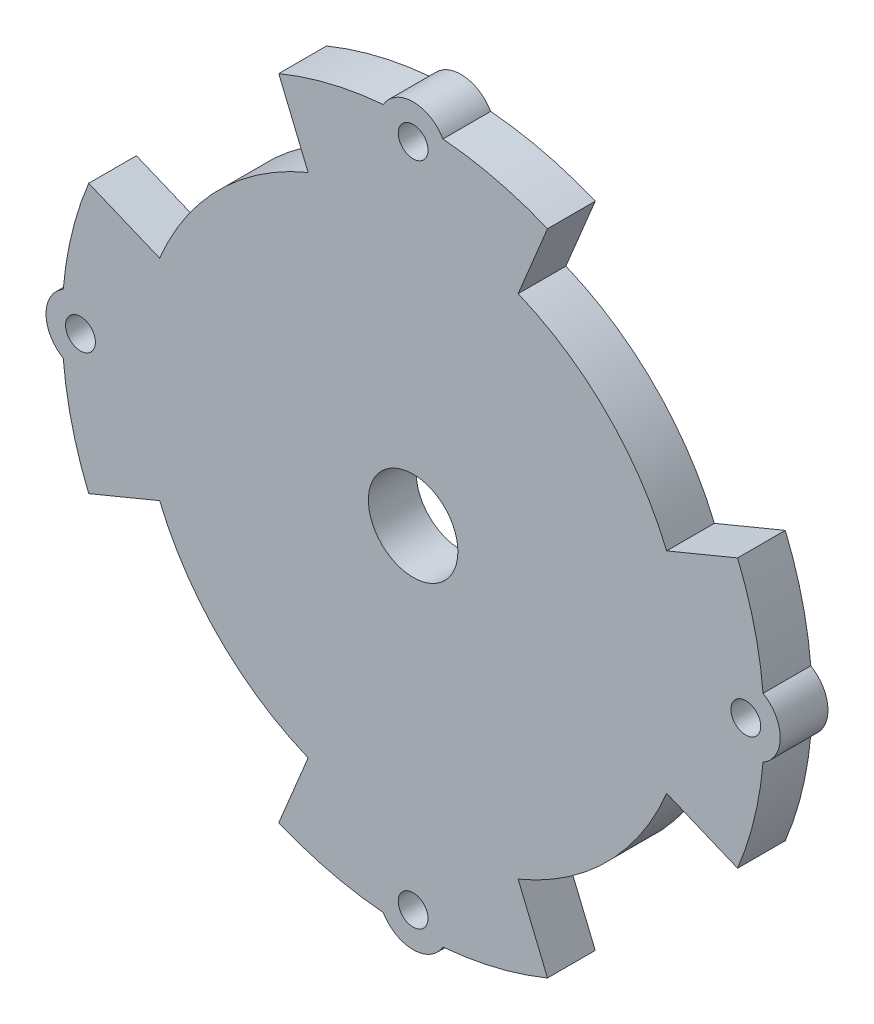
SolidWorks part; units mm, degrees
ref_plane "Front Plane" through (0, 0, 0) normal (0, 0, 1) x (1, 0, 0)
ref_plane "Top Plane" through (0, 0, 0) normal (0, 1, 0) x (1, 0, 0)
ref_plane "Right Plane" through (0, 0, 0) normal (1, 0, 0) x (0, 0, -1)
sketch "Sketch1" plane through (0, 0, 0) normal (0, 0, 1) x (1, 0, 0)
  line L0 (20, 0) -> (25, 0) construction
  line L1 (-20, 0) -> (-23, 0) construction
  line L2 (0, 25) -> (2.5, 26.4434) construction
  line L3 (2.5, 26.4434) -> (2.5, 29.3301) construction
  line L4 (2.5, 29.3301) -> (0, 30.7735) construction
  line L5 (0, 30.7735) -> (-2.5, 29.3301) construction
  line L6 (-2.5, 29.3301) -> (-2.5, 26.4434) construction
  line L7 (-2.5, 26.4434) -> (0, 25) construction
  line L8 (0, 0) -> (-20.8147, 20.8147) construction
  line L9 (0, 0) -> (0, 29.4365) construction
  line L10 (0, 0) -> (-27.1958, 11.2649) construction
  line L11 (-27.1958, 11.2649) -> (-11.2649, 27.1958) construction
  line L12 (-11.2649, 27.1958) -> (0, 0) construction
  line L13 (-27.1958, 11.2649) -> (-21.2492, 8.8017)
  line L14 (-11.2649, 27.1958) -> (-8.8017, 21.2492)
  line L15 (27.1958, 11.2649) -> (21.2492, 8.8017)
  line L16 (11.2649, 27.1958) -> (8.8017, 21.2492)
  line L17 (11.2649, -27.1958) -> (8.8017, -21.2492)
  line L18 (27.1958, -11.2649) -> (21.2492, -8.8017)
  line L19 (-27.1958, -11.2649) -> (-21.2492, -8.8017)
  line L20 (-11.2649, -27.1958) -> (-8.8017, -21.2492)
  circle A0 centre (0, 0) radius 20 construction
  circle A1 centre (0, 0) radius 25 construction
  circle A2 centre (0, 27.8868) radius 2.5 construction
  circle A3 centre (0, 0) radius 29.4365
  circle A4 centre (0, 27.8868) radius 1.25
  arc A5 (-2.5, 29.3301) -> (2.5, 29.3301) centre (0, 27.8868) cw
  circle A6 centre (27.8868, 0) radius 1.25
  arc A8 (29.3301, 2.5) -> (29.3301, -2.5) centre (27.8868, 0) cw
  arc A10 (8.8017, 21.2492) -> (21.2492, 8.8017) centre (0, 0) cw
  circle A12 centre (0, 0) radius 3.75
  circle A13 centre (0, 0) radius 23 construction
  arc A14 (-21.2492, 8.8017) -> (-8.8017, 21.2492) centre (0, 0) cw
  circle A15 centre (0, -27.8868) radius 1.25
  arc A16 (2.5, -29.3301) -> (-2.5, -29.3301) centre (0, -27.8868) cw
  arc A17 (21.2492, -8.8017) -> (8.8017, -21.2492) centre (0, 0) cw
  circle A18 centre (-27.8868, 0) radius 1.25
  arc A19 (-29.3301, -2.5) -> (-29.3301, 2.5) centre (-27.8868, 0) cw
  arc A20 (-8.8017, -21.2492) -> (-21.2492, -8.8017) centre (0, 0) cw
  point P16 (2.5, 27.8868)
  point P33 (-19.2303, 19.2303)
  dimension "D1" = 40
  dimension "D4" = 2.5
  dimension "D5" = 7.5
  dimension "D7" = 45
  dimension "D2" = 5
  dimension "D3" = 5
  dimension "D6" = 3
  dimension "D8" = 45
extrude "Boss-Extrude2" add sketch "Sketch1" along normal blind 4 contours A20 L20 A3 L17 A17 L18 L15 A10 L16 L14 A14 L13 L19 A18 A15 A12 A6 A4 | A5 A3 | A8 A3 | A16 A3 | A19 A3
